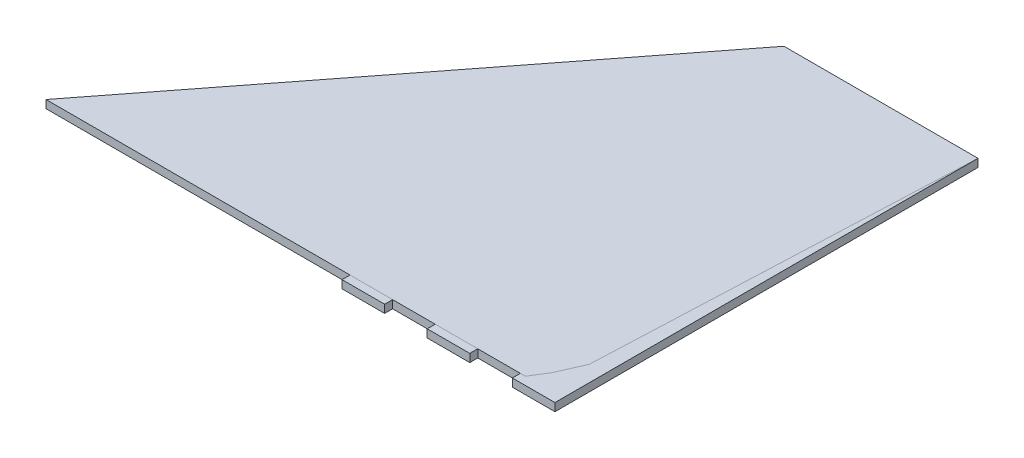
SolidWorks part; units mm, degrees
material "Foam#1"
ref_plane "Front Plane" through (0, 0, 0) normal (0, 0, 1) x (1, 0, 0)
ref_plane "Top Plane" through (0, 0, 0) normal (0, 1, 0) x (1, 0, 0)
ref_plane "Right Plane" through (0, 0, 0) normal (1, 0, 0) x (0, 0, -1)
sketch "Sketch1" plane through (0, 0, 0) normal (0, 1, 0) x (1, 0, 0)
  line L0 (0, 0) -> (279.4, 0)
  line L1 (279.4, 0) -> (279.4, 228.6)
  line L2 (279.4, 228.6) -> (177.8, 228.6)
  line L3 (0, 0) -> (177.8, 228.6)
  line L4 (279.4, 0) -> (177.8, 228.6)
  line L5 (279.4, 114.3) -> (288.925, 114.3)
  line L6 (288.925, -9.525) -> (288.925, 238.125)
  line L7 (88.9, 114.3) -> (81.3814, 120.1478)
  line L8 (81.3814, 120.1478) -> (-19.4752, -9.525)
  line L9 (288.925, -9.525) -> (-19.4752, -9.525)
  line L10 (81.3814, 120.1478) -> (173.1415, 238.125)
  line L11 (173.1415, 238.125) -> (288.925, 238.125)
  line L12 (222.7973, 111.721) -> (234.4027, 116.879)
  line L13 (222.7973, 111.721) -> (173.378, 222.9145)
  line L14 (222.7973, 111.721) -> (272.4511, 0)
  line L15 (234.4027, 116.879) -> (279.4, 15.6351)
  line L16 (234.4027, 116.879) -> (184.7489, 228.6)
  line L17 (288.925, -9.525) -> (288.925, -14.2875)
  line L18 (263.525, -9.525) -> (263.525, -14.2875)
  line L19 (238.125, -9.525) -> (238.125, -14.2875)
  line L20 (212.725, -9.525) -> (212.725, -14.2875)
  line L21 (187.325, -9.525) -> (187.325, -14.2875)
  line L22 (161.925, -9.525) -> (161.925, -14.2875)
  line L25 (288.925, -14.2875) -> (263.525, -14.2875)
  line L26 (238.125, -14.2875) -> (212.725, -14.2875)
  line L27 (187.325, -14.2875) -> (161.925, -14.2875)
  line L29 (288.925, -9.525) -> (263.525, -9.525)
  line L30 (238.125, -9.525) -> (212.725, -9.525)
  line L31 (187.325, -9.525) -> (161.925, -9.525)
  line L32 (139.7, -12.7) -> (114.3, -12.7)
  line L33 (136.525, -9.525) -> (136.525, -14.2875) [skipped]
  line L34 (111.125, -9.525) -> (111.125, -14.2875) [skipped]
  point P10 (288.925, 114.3)
  point P17 (228.6, 114.3)
  dimension "D1" = 279.4
  dimension "D2" = 228.6
  dimension "D3" = 101.6
  dimension "D4" = 9.525
  dimension "D5" = 247.65
  dimension "D6" = 9.525
  dimension "D7" = 12.7
  dimension "D8" = 4.7625
  dimension "D9" = 8
extrude "Boss-Extrude1" add sketch "Sketch1" along normal blind 4.7625 contours L9 L6 L5 L1 L0 L3 L7 L8 | L11 L10 L7 L3 L2 L1 L5 L6 | L12 L16 L2 L4 | L13 L12 L4 L3 | L15 L12 L4 L1 | L12 L14 L0 L4
sketch "Sketch2" plane through (0, 4.7625, 0) normal (0, 1, 0) x (1, 0, 0)
  line L0 (-19.4752, -9.525) -> (288.925, -9.525)
  line L1 (288.925, -14.2875) -> (288.925, 238.125) construction
  line L2 (288.925, -9.525) -> (288.925, 238.125)
  line L3 (288.925, 238.125) -> (173.1415, 238.125)
  line L4 (173.1415, 238.125) -> (-19.4752, -9.525)
  point P5 (0, 0)
  point P11 (0, 0)
surface "Surface-Plane1" sketch "Sketch2"
sketch "Sketch3" plane through (0, 0, 0) normal (0, -1, 0) x (1, 0, 0)
  line L0 (-19.4752, 9.525) -> (173.1415, -238.125)
  line L1 (173.1415, -238.125) -> (288.925, -238.125)
  line L2 (288.925, -238.125) -> (288.925, 9.525)
  line L3 (288.925, 9.525) -> (-19.4752, 9.525)
  point P4 (0, 0)
surface "Surface-Plane2" sketch "Sketch3"
